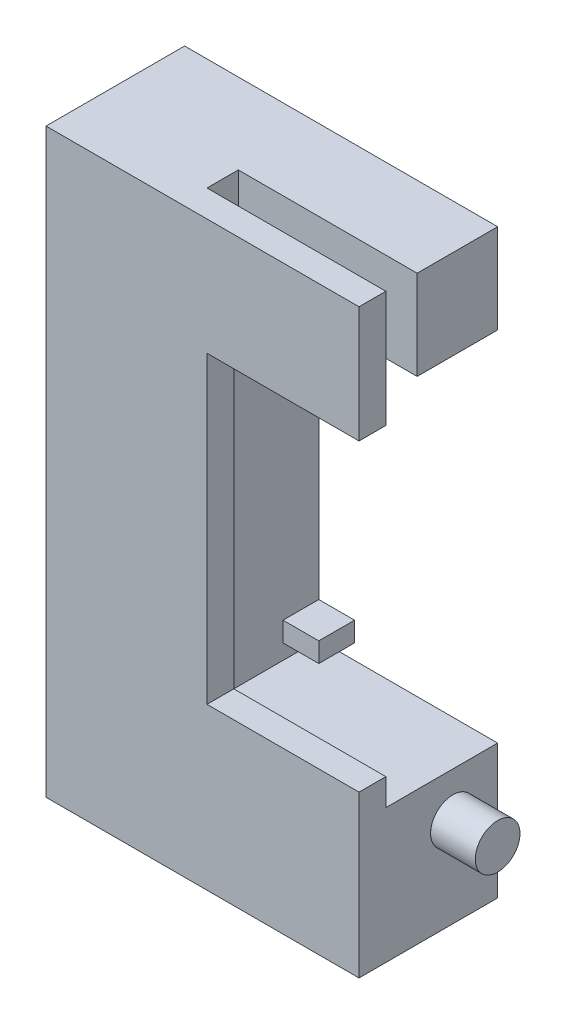
SolidWorks part; units mm, degrees
material "PVC 0.007 Plasticized"
ref_plane "Front Plane" through (0, 0, 0) normal (0, 0, 1) x (1, 0, 0)
ref_plane "Top Plane" through (0, 0, 0) normal (0, 1, 0) x (1, 0, 0)
ref_plane "Right Plane" through (0, 0, 0) normal (1, 0, 0) x (0, 0, -1)
sketch "Sketch1" plane through (0, 0, 0) normal (0, 0, 1) x (1, 0, 0)
  line L0 (0, 0) -> (0, 65)
  line L1 (0, 65) -> (35, 65)
  line L2 (35, 65) -> (35, 55)
  line L3 (35, 55) -> (15, 55)
  line L4 (15, 55) -> (15, 15)
  line L5 (15, 15) -> (35, 15)
  line L6 (35, 15) -> (35, 0)
  line L7 (35, 0) -> (0, 0)
  dimension "D1" = 40
  dimension "D2" = 15
  dimension "D3" = 10
  dimension "D4" = 20
  dimension "D5" = 15
  dimension "D6" = 65
  dimension "D7" = 35
extrude "Boss-Extrude1" add sketch "Sketch1" along normal blind 8.5 and the other way blind 4
ref_plane "Plane1" through (0, 65, 0) normal (0, 1, 0) x (1, 0, 0)
sketch "Sketch3" plane through (0, 65, 0) normal (0, 1, 0) x (1, 0, 0)
  line L0 (35, -8.5) -> (0, -8.5) construction
  line L1 (15, -5) -> (55, -5)
  line L2 (15, -5) -> (15, -8.5)
  line L3 (15, -8.5) -> (55, -8.5)
  line L4 (55, -5) -> (55, -8.5)
  line L5 (0, -8.5) -> (0, 4) construction
  dimension "D1" = 15
  dimension "D2" = 3.5
  dimension "D3" = 40
extrude "Cut-Extrude1" cut sketch "Sketch3" against normal blind 10
ref_plane "Plane2" through (0, 0, 8.5) normal (0, 0, 1) x (1, 0, 0)
sketch "Sketch4" plane through (0, 0, 8.5) normal (0, 0, 1) x (1, 0, 0)
  line L0 (35, 0) -> (0, 0)
  line L1 (0, 0) -> (0, 65)
  line L2 (6.875, 65) -> (-6.875, 65) construction
  line L3 (0, 65) -> (0, 0) construction
  line L4 (0, 65) -> (35, 65)
  line L5 (35, 65) -> (35, 52)
  line L6 (35, 52) -> (18, 52)
  line L7 (18, 52) -> (18, 18)
  line L8 (18, 18) -> (35, 18)
  line L9 (35, 18) -> (35, 0)
  line L11 (15, 15) -> (15, 65) construction
  line L12 (35, 15) -> (15, 15) construction
  dimension "D2" = 3
  dimension "D3" = 3
  dimension "D4" = 65
  dimension "D5" = 35
  dimension "D6" = 35
extrude "Boss-Extrude2" add sketch "Sketch4" along normal blind 3
ref_plane "Plane3" through (35, 0, 0) normal (1, 0, 0) x (0, 0, -1)
sketch "Sketch5" plane through (35, 0, 0) normal (1, 0, 0) x (0, 0, -1)
  line L0 (4, 0) -> (4, 15) construction
  line L1 (-8.5, 15) -> (4, 15) construction
  circle A0 centre (-1, 10) radius 2.5
  dimension "D3" = 5
  dimension "D1" = 5
  dimension "D2" = 5
extrude "Boss-Extrude3" add sketch "Sketch5" along normal blind 5
ref_plane "Plane4" through (15, 0, 0) normal (1, 0, 0) x (0, 0, -1)
sketch "Sketch6" plane through (15, 0, 0) normal (1, 0, 0) x (0, 0, -1)
  line L0 (4, 15) -> (4, 55) construction
  line L1 (4, 53.3) -> (0, 53.3)
  line L2 (4, 53.3) -> (4, 51.1)
  line L3 (4, 51.1) -> (0, 51.1)
  line L4 (0, 53.3) -> (0, 51.1)
  line L5 (4, 15) -> (-8.5, 15) construction
  line L6 (4, 16.7) -> (0, 16.7)
  line L7 (4, 16.7) -> (4, 18.9)
  line L8 (4, 18.9) -> (0, 18.9)
  line L9 (0, 16.7) -> (0, 18.9)
  line L10 (4, 55) -> (-5, 55) construction
  dimension "D1" = 4
  dimension "D2" = 2.2
  dimension "D3" = 1.7
  dimension "D4" = 1.7
  dimension "D5" = 2.2
  dimension "D6" = 4
extrude "Boss-Extrude4" add sketch "Sketch6" along normal blind 4
